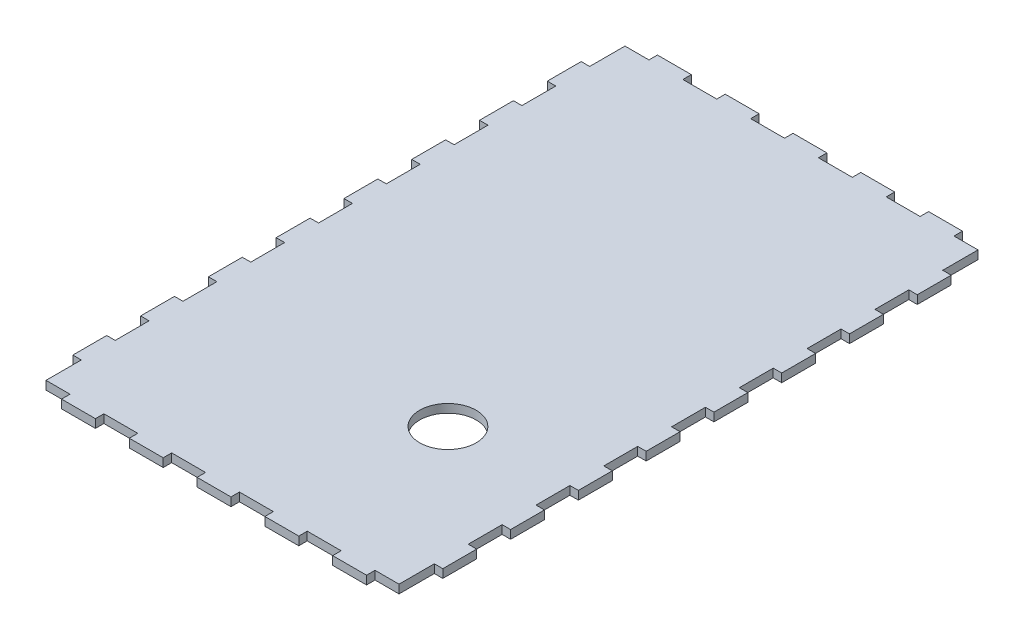
SolidWorks part; units mm, degrees
ref_plane "Front Plane" through (0, 0, 0) normal (0, 0, 1) x (1, 0, 0)
ref_plane "Top Plane" through (0, 0, 0) normal (0, 1, 0) x (1, 0, 0)
ref_plane "Right Plane" through (0, 0, 0) normal (1, 0, 0) x (0, 0, -1)
sketch "Sketch3" plane through (0, 0, 0) normal (0, 1, 0) x (1, 0, 0)
  line L231 (-62.5, -102.5) -> (62.5, -102.5)
  line L232 (-62.5, -102.5) -> (-62.5, 102.5)
  line L233 (-62.5, 102.5) -> (62.5, 102.5)
  line L234 (62.5, -102.5) -> (62.5, 102.5)
  line L235 (-62.5, -102.5) -> (62.5, 102.5) construction
  line L236 (-62.5, 102.5) -> (62.5, -102.5) construction
  point P66 (0, 0)
  dimension "D3" = 205
  dimension "D4" = 125
extrude "Boss-Extrude1" add sketch "Sketch3" along normal blind 3
sketch "Sketch5" plane through (0, 3, 0) normal (0, 1, 0) x (1, 0, 0)
  line L0 (62.5, 102.5) -> (-62.5, 102.5) construction
  line L1 (-54, 102.5) -> (-42, 102.5)
  line L2 (-54, 102.5) -> (-54, 105.5)
  line L3 (-54, 105.5) -> (-42, 105.5)
  line L4 (-42, 102.5) -> (-42, 105.5)
  line L5 (-30, 102.5) -> (-30, 105.5)
  line L6 (-30, 102.5) -> (-18, 102.5)
  line L7 (-18, 102.5) -> (-18, 105.5)
  line L8 (-30, 105.5) -> (-18, 105.5)
  line L9 (-6, 102.5) -> (-6, 105.5)
  line L10 (-6, 102.5) -> (6, 102.5)
  line L11 (6, 102.5) -> (6, 105.5)
  line L12 (-6, 105.5) -> (6, 105.5)
  line L13 (18, 102.5) -> (18, 105.5)
  line L14 (18, 102.5) -> (30, 102.5)
  line L15 (30, 102.5) -> (30, 105.5)
  line L16 (18, 105.5) -> (30, 105.5)
  line L17 (42, 102.5) -> (42, 105.5)
  line L18 (42, 102.5) -> (54, 102.5)
  line L19 (54, 102.5) -> (54, 105.5)
  line L20 (42, 105.5) -> (54, 105.5)
  line L41 (-62.5, 102.5) -> (-62.5, -102.5) construction
  line L43 (62.5, -102.5) -> (62.5, 102.5) construction
  line L44 (-62.5, 90) -> (-65.5, 90)
  line L45 (-62.5, 90) -> (-62.5, 78)
  line L46 (-62.5, 78) -> (-65.5, 78)
  line L47 (-65.5, 90) -> (-65.5, 78)
  line L48 (65.5, 90) -> (65.5, 78)
  line L49 (65.5, 90) -> (62.5, 90)
  line L50 (62.5, 90) -> (62.5, 78)
  line L51 (65.5, 78) -> (62.5, 78)
  line L52 (65.5, 66) -> (65.5, 54)
  line L53 (65.5, 66) -> (62.5, 66)
  line L54 (62.5, 66) -> (62.5, 54)
  line L55 (65.5, 54) -> (62.5, 54)
  line L56 (65.5, 42) -> (65.5, 30)
  line L57 (65.5, 42) -> (62.5, 42)
  line L58 (62.5, 42) -> (62.5, 30)
  line L59 (65.5, 30) -> (62.5, 30)
  line L60 (65.5, 18) -> (65.5, 6)
  line L61 (65.5, 18) -> (62.5, 18)
  line L62 (62.5, 18) -> (62.5, 6)
  line L63 (65.5, 6) -> (62.5, 6)
  line L64 (65.5, -6) -> (65.5, -18)
  line L65 (65.5, -6) -> (62.5, -6)
  line L66 (62.5, -6) -> (62.5, -18)
  line L67 (65.5, -18) -> (62.5, -18)
  line L68 (65.5, -30) -> (65.5, -42)
  line L69 (65.5, -30) -> (62.5, -30)
  line L70 (62.5, -30) -> (62.5, -42)
  line L71 (65.5, -42) -> (62.5, -42)
  line L72 (65.5, -54) -> (65.5, -66)
  line L73 (65.5, -54) -> (62.5, -54)
  line L74 (62.5, -54) -> (62.5, -66)
  line L75 (65.5, -66) -> (62.5, -66)
  line L76 (65.5, -78) -> (65.5, -90)
  line L77 (65.5, -78) -> (62.5, -78)
  line L78 (62.5, -78) -> (62.5, -90)
  line L79 (65.5, -90) -> (62.5, -90)
  line L80 (-62.5, 66) -> (-62.5, 54)
  line L81 (-62.5, 66) -> (-65.5, 66)
  line L82 (-65.5, 66) -> (-65.5, 54)
  line L83 (-62.5, 54) -> (-65.5, 54)
  line L84 (-62.5, 42) -> (-62.5, 30)
  line L85 (-62.5, 42) -> (-65.5, 42)
  line L86 (-65.5, 42) -> (-65.5, 30)
  line L87 (-62.5, 30) -> (-65.5, 30)
  line L88 (-62.5, 18) -> (-62.5, 6)
  line L89 (-62.5, 18) -> (-65.5, 18)
  line L90 (-65.5, 18) -> (-65.5, 6)
  line L91 (-62.5, 6) -> (-65.5, 6)
  line L92 (-62.5, -6) -> (-62.5, -18)
  line L93 (-62.5, -6) -> (-65.5, -6)
  line L94 (-65.5, -6) -> (-65.5, -18)
  line L95 (-62.5, -18) -> (-65.5, -18)
  line L96 (-62.5, -30) -> (-62.5, -42)
  line L97 (-62.5, -30) -> (-65.5, -30)
  line L98 (-65.5, -30) -> (-65.5, -42)
  line L99 (-62.5, -42) -> (-65.5, -42)
  line L100 (-62.5, -54) -> (-62.5, -66)
  line L101 (-62.5, -54) -> (-65.5, -54)
  line L102 (-65.5, -54) -> (-65.5, -66)
  line L103 (-62.5, -66) -> (-65.5, -66)
  line L104 (-62.5, -78) -> (-62.5, -90)
  line L105 (-62.5, -78) -> (-65.5, -78)
  line L106 (-65.5, -78) -> (-65.5, -90)
  line L107 (-62.5, -90) -> (-65.5, -90)
  line L108 (-62.5, 6) -> (-62.5, -6)
  line L109 (-54, -105.5) -> (-54, -102.5)
  line L110 (-54, -105.5) -> (-42, -105.5)
  line L111 (-42, -105.5) -> (-42, -102.5)
  line L112 (-54, -102.5) -> (-42, -102.5)
  line L113 (-30, -105.5) -> (-30, -102.5)
  line L114 (-30, -105.5) -> (-18, -105.5)
  line L115 (-18, -105.5) -> (-18, -102.5)
  line L116 (-30, -102.5) -> (-18, -102.5)
  line L117 (-6, -105.5) -> (-6, -102.5)
  line L118 (-6, -105.5) -> (6, -105.5)
  line L119 (6, -105.5) -> (6, -102.5)
  line L120 (-6, -102.5) -> (6, -102.5)
  line L121 (18, -105.5) -> (18, -102.5)
  line L122 (18, -105.5) -> (30, -105.5)
  line L123 (30, -105.5) -> (30, -102.5)
  line L124 (18, -102.5) -> (30, -102.5)
  line L125 (42, -105.5) -> (42, -102.5)
  line L126 (42, -105.5) -> (54, -105.5)
  line L127 (54, -105.5) -> (54, -102.5)
  line L128 (42, -102.5) -> (54, -102.5)
  point P6 (0, 102.5)
  point P55 (-62.5, 0)
  line M6 (62.5, -102.5) -> (62.5, 102.5)
  line M7 (62.5, 102.5) -> (-62.5, 102.5)
  line M8 (-62.5, 102.5) -> (-62.5, -102.5)
  line M9 (-62.5, -102.5) -> (62.5, -102.5)
  dimension "D1" = 12
  dimension "D2" = 3
  dimension "D5" = 12
  dimension "D6" = 205
  dimension "D8" = 12
  dimension "D9" = 3
  dimension "D12" = 125
  dimension "D13" = 24
  dimension "D3" = 5
  dimension "D4" = 2
  dimension "D10" = 2
  dimension "D11" = 8
extrude "Boss-Extrude2" add sketch "Sketch5" against normal blind 3 contours L122 L123 L121 M9 | L118 L119 L117 M9 | L107 L105 L106 M8 | L103 L101 L102 M8 | L95 L93 L94 M8 | L79 L76 L77 M6 | L71 L68 L69 M6 | L67 L64 L65 M6 | L63 L60 L61 M6 | L59 L56 L57 M6 | L51 L48 L49 M6 | L16 L13 L15 M7 | L12 L9 L11 M7 | L8 L5 L7 M7 | L4 L3 L2 M7 | L87 L85 L86 M8 | L91 L89 L90 M8 | L128 L127 L126 L125 | L116 L115 L114 L113 | L112 L111 L110 L109 | L98 L99 L96 L97 | L74 L75 L72 L73 | L52 L55 L54 L53 | L20 L19 L18 L17 | L45 L46 L47 L44 | L82 L83 L80 L81
sketch "Sketch6" plane through (0, 3, 0) normal (0, 1, 0) x (1, 0, 0)
  line L0 (-6, -105.5) -> (6, -105.5) construction
  line L2 (62.5, -48) -> (32.5, -48)
  line L3 (62.5, -54) -> (62.5, -42) construction
  circle A0 centre (22.8175, -45.5) radius 10
  dimension "D1" = 20
  dimension "D2" = 60
  dimension "D3" = 30
extrude "Cut-Extrude1" cut sketch "Sketch6" against normal blind 6 contours A0
